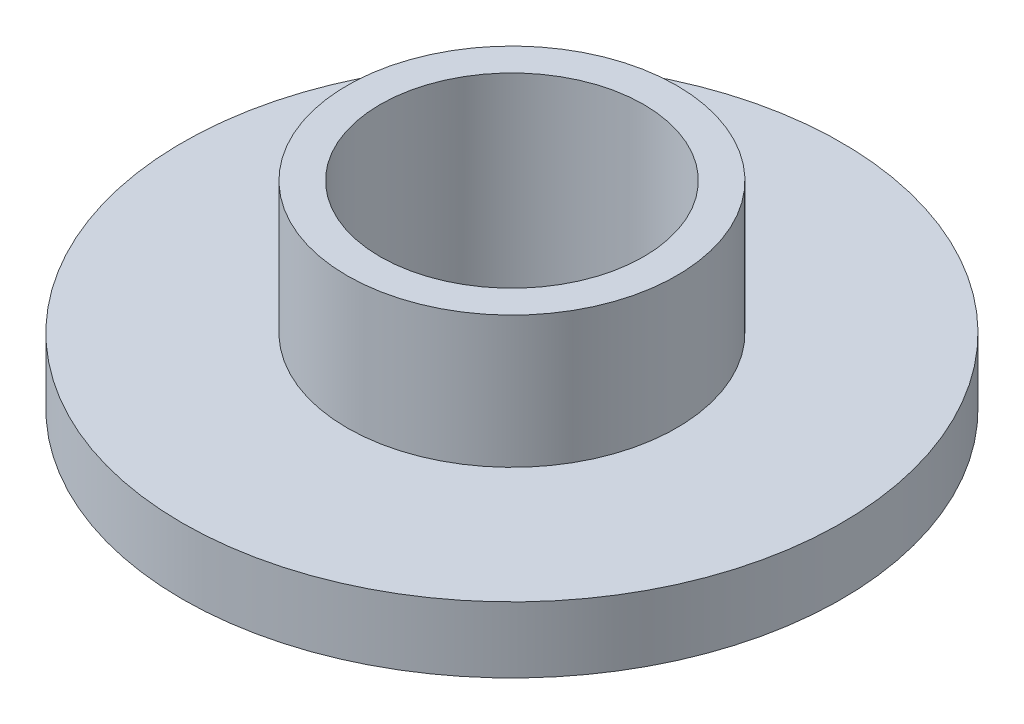
SolidWorks part; units mm, degrees
ref_plane "Front Plane" through (0, 0, 0) normal (0, 0, 1) x (1, 0, 0)
ref_plane "Top Plane" through (0, 0, 0) normal (0, 1, 0) x (1, 0, 0)
ref_plane "Right Plane" through (0, 0, 0) normal (1, 0, 0) x (0, 0, -1)
sketch "Sketch1" plane through (0, 0, 0) normal (0, 1, 0) x (1, 0, 0)
  circle A0 centre (0, 0) radius 7.9375
  circle A1 centre (0, 0) radius 3.175
  dimension "D1" = 15.875
  dimension "D2" = 6.35
extrude "Boss-Extrude1" add sketch "Sketch1" along normal blind 1.5875 contours A1 | A0
sketch "Sketch2" plane through (0, 1.5875, 0) normal (0, 1, 0) x (1, 0, 0)
  circle A0 centre (0, 0) radius 3.175
  circle A1 centre (0, 0) radius 3.9688
  dimension "D1" = 7.9375
  dimension "D2" = 6.35
extrude "Boss-Extrude2" add sketch "Sketch2" along normal blind 3.175
sketch "Sketch3" plane through (0, 0, 0) normal (0, -1, 0) x (1, 0, 0)
  circle A0 centre (0, 0) radius 3.175
  circle A1 centre (0, 0) radius 3.937
  dimension "D1" = 7.874
  dimension "D2" = 6.35
extrude "Boss-Extrude3" add sketch "Sketch3" along normal blind 0.7937
